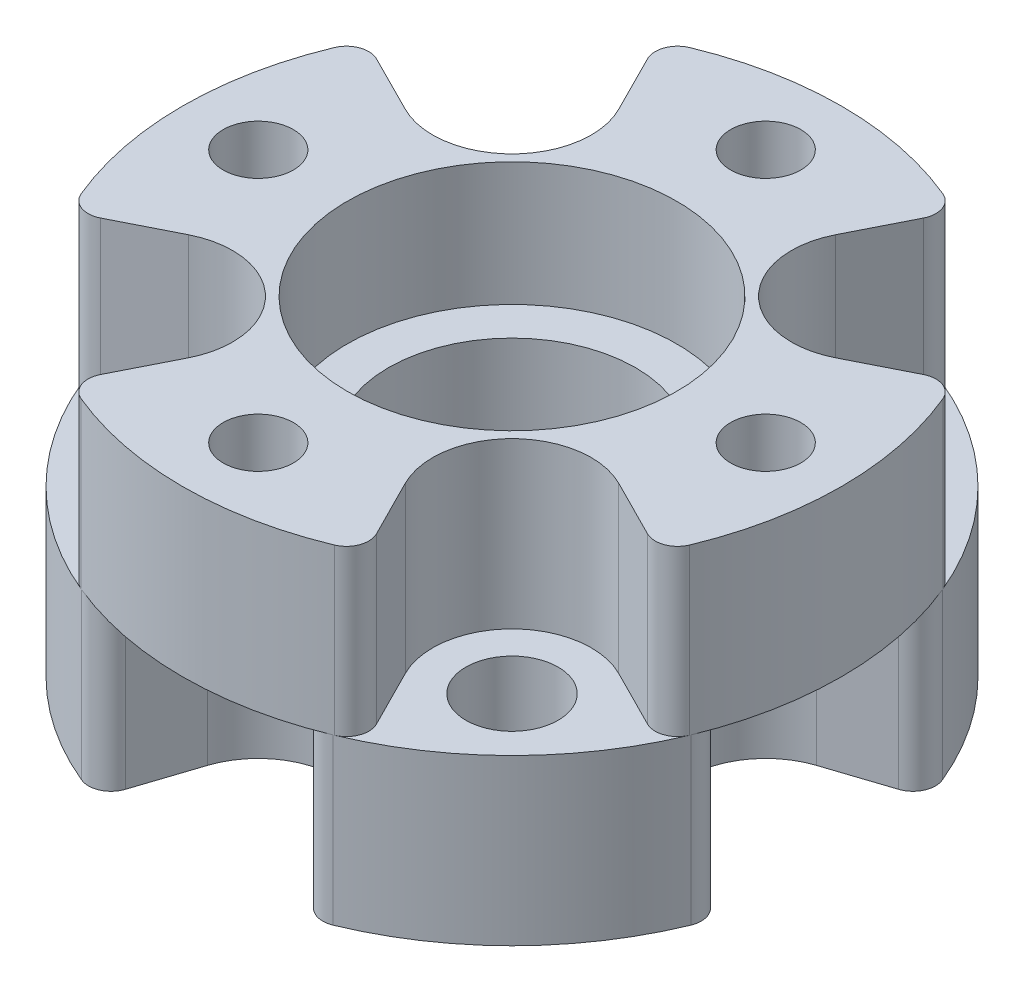
SolidWorks part; units mm, degrees
ref_plane "Front Plane" through (0, 0, 0) normal (0, 0, 1) x (1, 0, 0)
ref_plane "Top Plane" through (0, 0, 0) normal (0, 1, 0) x (1, 0, 0)
ref_plane "Right Plane" through (0, 0, 0) normal (1, 0, 0) x (0, 0, -1)
sketch "Sketch1" plane through (0, 0, 0) normal (0, 0, 1) x (1, 0, 0)
  line L0 (12.7, 12.7) -> (0, 12.7)
  line L1 (0, 12.7) -> (0, 0)
  line L2 (0, 0) -> (12.7, 0)
  line L3 (12.7, 0) -> (12.7, 12.7)
  line L4 (0, 12.7) -> (0, 0) construction
revolve "Revolve1" add sketch "Sketch1" angle 360 about L4
sketch "Sketch2" plane through (0, 12.7, 0) normal (0, 1, 0) x (-1, 0, 0)
  line L0 (-5.7191, -11.3394) -> (-4.1826, -8.2928)
  line L1 (-8.2928, -4.1826) -> (-11.3394, -5.7191)
  arc A0 (-4.1826, -8.2928) -> (-8.2928, -4.1826) centre (-6.9148, -6.9148) ccw
  arc A1 (-11.3394, -5.7191) -> (-5.7191, -11.3394) centre (0, 0) ccw
extrude "Cut-Extrude1" cut sketch "Sketch2" against normal blind 6.35
sketch "Sketch3" plane through (0, 12.7, 0) normal (0, 1, 0) x (-1, 0, 0)
  line L0 (-11.3394, 5.7191) -> (-8.2928, 4.1826)
  line L1 (-4.1826, 8.2928) -> (-5.7191, 11.3394)
  arc A0 (-8.2928, 4.1826) -> (-4.1826, 8.2928) centre (-6.9148, 6.9148) ccw
  arc A1 (-5.7191, 11.3394) -> (-11.3394, 5.7191) centre (0, 0) ccw
extrude "Cut-Extrude2" cut sketch "Sketch3" against normal blind 6.35
sketch "Sketch4" plane through (0, 0, 0) normal (0, -1, 0) x (1, 0, 0)
  line L0 (12.0622, 3.9741) -> (8.8214, 2.9064)
  line L1 (8.8214, -2.9064) -> (12.0622, -3.9741)
  arc A0 (8.8214, 2.9064) -> (8.8214, -2.9064) centre (9.779, 0) ccw
  arc A1 (12.0622, -3.9741) -> (12.0622, 3.9741) centre (0, 0) ccw
extrude "Cut-Extrude3" cut sketch "Sketch4" against normal blind 6.35
sketch "Sketch5" plane through (0, 12.7, 0) normal (0, 1, 0) x (-1, 0, 0)
  line L0 (5.7191, 11.3394) -> (4.1826, 8.2928)
  line L1 (8.2928, 4.1826) -> (11.3394, 5.7191)
  arc A0 (4.1826, 8.2928) -> (8.2928, 4.1826) centre (6.9148, 6.9148) ccw
  arc A1 (11.3394, 5.7191) -> (5.7191, 11.3394) centre (0, 0) ccw
extrude "Cut-Extrude4" cut sketch "Sketch5" against normal blind 6.35
sketch "Sketch6" plane through (0, 12.7, 0) normal (0, 1, 0) x (-1, 0, 0)
  line L0 (11.3394, -5.7191) -> (8.2928, -4.1826)
  line L1 (4.1826, -8.2928) -> (5.7191, -11.3394)
  arc A0 (8.2928, -4.1826) -> (4.1826, -8.2928) centre (6.9148, -6.9148) ccw
  arc A1 (5.7191, -11.3394) -> (11.3394, -5.7191) centre (0, 0) ccw
extrude "Cut-Extrude5" cut sketch "Sketch6" against normal blind 6.35
sketch "Sketch7" plane through (0, 0, 0) normal (0, -1, 0) x (1, 0, 0)
  line L0 (3.9741, -12.0622) -> (2.9064, -8.8214)
  line L1 (-2.9064, -8.8214) -> (-3.9741, -12.0622)
  arc A0 (2.9064, -8.8214) -> (-2.9064, -8.8214) centre (0, -9.779) ccw
  arc A1 (-3.9741, -12.0622) -> (3.9741, -12.0622) centre (0, 0) ccw
extrude "Cut-Extrude6" cut sketch "Sketch7" against normal blind 6.35
sketch "Sketch8" plane through (0, 0, 0) normal (0, -1, 0) x (1, 0, 0)
  line L0 (-12.0622, -3.9741) -> (-8.8214, -2.9064)
  line L1 (-8.8214, 2.9064) -> (-12.0622, 3.9741)
  arc A0 (-8.8214, -2.9064) -> (-8.8214, 2.9064) centre (-9.779, 0) ccw
  arc A1 (-12.0622, 3.9741) -> (-12.0622, -3.9741) centre (0, 0) ccw
extrude "Cut-Extrude7" cut sketch "Sketch8" against normal blind 6.35
sketch "Sketch9" plane through (0, 0, 0) normal (0, -1, 0) x (1, 0, 0)
  line L0 (-3.9741, 12.0622) -> (-2.9064, 8.8214)
  line L1 (2.9064, 8.8214) -> (3.9741, 12.0622)
  arc A0 (-2.9064, 8.8214) -> (2.9064, 8.8214) centre (0, 9.779) ccw
  arc A1 (3.9741, 12.0622) -> (-3.9741, 12.0622) centre (0, 0) ccw
extrude "Cut-Extrude8" cut sketch "Sketch9" against normal blind 6.35
ref_plane "Plane1" through (0, 0, 0) normal (0, 0, -1) x (-1, 0, 0)
sketch "Sketch10" plane through (0, 0, 0) normal (0, 0, -1) x (-1, 0, 0)
  line L0 (-6.35, 0) -> (0, 0)
  line L1 (0, 0) -> (0, 12.7)
  line L2 (0, 12.7) -> (-6.35, 12.7)
  line L3 (-6.35, 12.7) -> (-6.35, 7.9375)
  line L4 (-6.35, 7.9375) -> (-4.7625, 7.9375)
  line L5 (-4.7625, 7.9375) -> (-4.7625, 4.7625)
  line L6 (-4.7625, 4.7625) -> (-6.35, 4.7625)
  line L7 (-6.35, 4.7625) -> (-6.35, 0)
  line L8 (0, 0) -> (0, 12.7) construction
revolve "Cut-Revolve1" cut sketch "Sketch10" angle 360 about L8
hole_wizard "M3 Clearance Hole1" positions "Sketch12" profile "Sketch11" hole size "M3" standard "ANSI Metric"
sketch "Sketch12" plane through (0, 6.35, 0) normal (0, 1, 0) x (1, 0, 0)
  point P0 (6.9148, 6.9148)
  point P1 (-6.9148, 6.9148)
  point P2 (-6.9148, -6.9148)
  point P3 (6.9148, -6.9148)
sketch "Sketch11" plane through (6.9148, 6.35, -6.9148) normal (1, 0, 0) x (0, 0, 1)
  line L0 (0, 0) -> (0, 6.35)
  line L1 (0, 6.35) -> (1.778, 6.35)
  line L2 (1.778, 6.35) -> (1.778, 0)
  line L5 (1.778, 0) -> (0, 0)
  line L11 (0, -6.35) -> (0, 107.95) construction
  dimension "Thru Hole Dia." = 3.556
  dimension "Thru Hole Depth" = 6.35
hole_wizard "M2.5 Clearance Hole1" positions "Sketch14" profile "Sketch13" hole size "M2.5" standard "ANSI Metric"
sketch "Sketch14" plane through (0, 6.35, 0) normal (0, -1, 0) x (-1, 0, 0)
  point P0 (-9.779, 0)
  point P1 (0, 9.779)
  point P2 (9.779, 0)
  point P3 (0, -9.779)
sketch "Sketch13" plane through (9.779, 6.35, 0) normal (1, 0, 0) x (0, 0, -1)
  line L0 (0, 0) -> (0, 6.35)
  line L1 (0, 6.35) -> (1.3525, 6.35)
  line L2 (1.3525, 6.35) -> (1.3525, 0)
  line L5 (1.3525, 0) -> (0, 0)
  line L11 (0, -6.35) -> (0, 107.95) construction
  dimension "Thru Hole Dia." = 2.7051
  dimension "Thru Hole Depth" = 6.35
fillet "Fillet1" radius 0.8636 16 edges at (-3.9741, 3.175, 12.0622) (-5.7191, 9.525, -11.3394) (-11.3394, 9.525, 5.7191) (12.0622, 3.175, 3.9741) (-12.0622, 3.175, -3.9741) (12.0622, 3.175, -3.9741) (-5.7191, 9.525, 11.3394) (3.9741, 3.175, -12.0622) (-11.3394, 9.525, -5.7191) (5.7191, 9.525, -11.3394) (-3.9741, 3.175, -12.0622) (11.3394, 9.525, -5.7191) (-12.0622, 3.175, 3.9741) (11.3394, 9.525, 5.7191) (3.9741, 3.175, 12.0622) (5.7191, 9.525, 11.3394)
